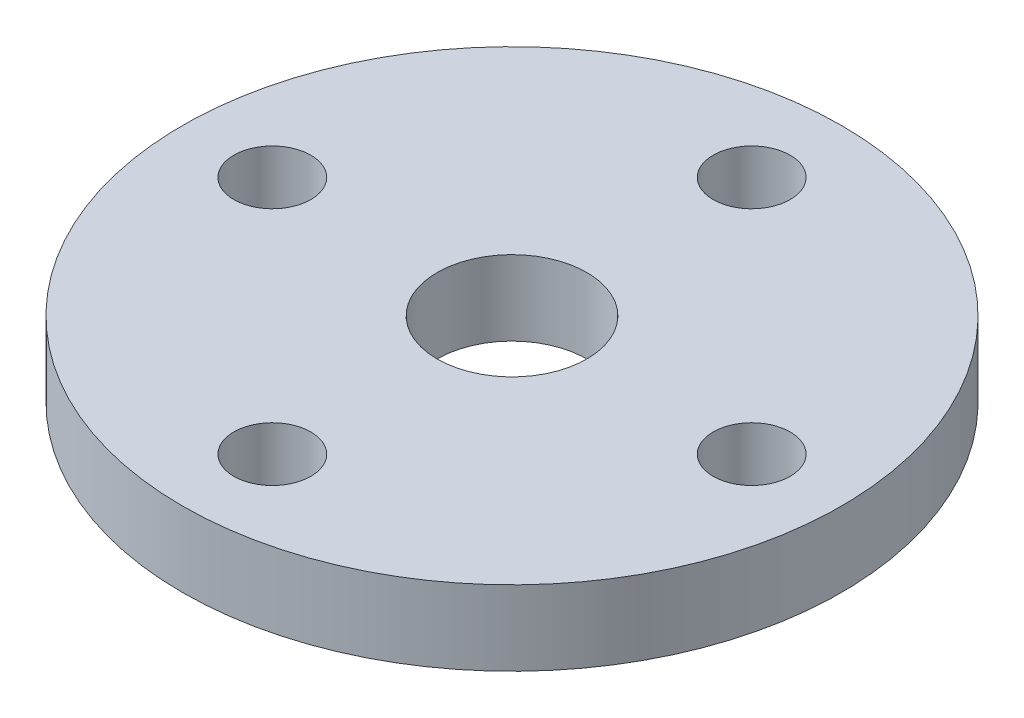
SolidWorks part; units mm, degrees
ref_plane "Front Plane" through (0, 0, 0) normal (0, 0, 1) x (1, 0, 0)
ref_plane "Top Plane" through (0, 0, 0) normal (0, 1, 0) x (1, 0, 0)
ref_plane "Right Plane" through (0, 0, 0) normal (1, 0, 0) x (0, 0, -1)
sketch "Sketch1" plane through (0, 0, 0) normal (0, 1, 0) x (1, 0, 0)
  circle A0 centre (0, 0) radius 13.97
  dimension "D1" = 27.94
extrude "Boss-Extrude1" add sketch "Sketch1" along normal blind 3.175
sketch "Sketch2" plane through (0, 3.175, 0) normal (0, 1, 0) x (1, 0, 0)
  circle A0 centre (0, 0) radius 3.175
  dimension "D1" = 6.35
extrude "Cut-Extrude1" cut sketch "Sketch2" against normal blind 3.175
hole_wizard "#4 Clearance Hole1" positions "Sketch4" profile "Sketch3" hole size "#4" standard "ANSI Inch"
sketch "Sketch4" plane through (0, 3.175, 0) normal (0, 1, 0) x (1, 0, 0)
  point P0 (0, 10.16)
  dimension "D1" = 10.16
sketch "Sketch3" plane through (0, 3.175, -10.16) normal (1, 0, 0) x (0, 0, 1)
  line L0 (0, 0) -> (0, 11.1406)
  line L1 (0, 11.1406) -> (1.6319, 10.16)
  line L2 (1.6319, 10.16) -> (1.6319, 0)
  line L5 (1.6319, 0) -> (0, 0)
  line L10 (0, 11.1406) -> (-1.6319, 10.16) construction
  line L11 (0, -6.35) -> (0, 107.95) construction
  dimension "Hole Dia." = 3.2639
  dimension "Hole Depth" = 10.16
  dimension "Drill Angle" = 118
pattern_circular "CirPattern1" count 4 over 360 about axis through (0, 0, 0) along (0, 1, 0) of "#4 Clearance Hole1"
